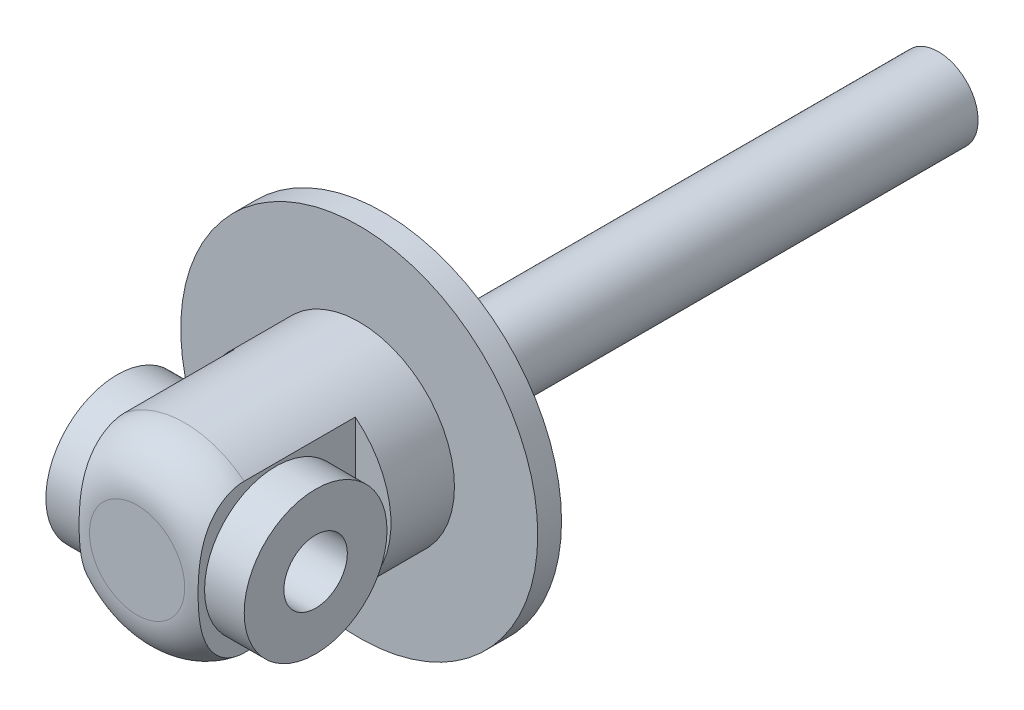
SolidWorks part; units mm, degrees
ref_plane "Front Plane" through (0, 0, 0) normal (0, 0, 1) x (1, 0, 0)
ref_plane "Top Plane" through (0, 0, 0) normal (0, 1, 0) x (1, 0, 0)
ref_plane "Right Plane" through (0, 0, 0) normal (1, 0, 0) x (0, 0, -1)
sketch "Sketch1" plane through (0, 0, 0) normal (0, 0, 1) x (1, 0, 0)
  circle A0 centre (0, 0) radius 22.5
  dimension "D1" = 45
extrude "Boss-Extrude1" add sketch "Sketch1" against normal blind 3
sketch "Sketch2" plane through (0, 0, -3) normal (0, 0, -1) x (-1, 0, 0)
  circle A0 centre (0, 0) radius 5
  dimension "D1" = 10
extrude "Boss-Extrude2" add sketch "Sketch2" along normal blind 70
sketch "Sketch3" plane through (0, 0, 0) normal (0, 0, 1) x (1, 0, 0)
  circle A0 centre (0, 0) radius 12
  dimension "D1" = 24
extrude "Boss-Extrude3" add sketch "Sketch3" along normal blind 28
fillet "Fillet1" radius 6 1 edges at (12, 0, 28)
sketch "Sketch4" plane through (0, 0, 0) normal (0, 1, 0) x (1, 0, 0)
  line L0 (0, 0) -> (0, -33.2547) construction
  line L1 (7.5, -28) -> (27.07, -28)
  line L2 (-6, -28) -> (6, -28) construction
  line L3 (27.07, -28) -> (27.07, -8)
  line L4 (27.07, -8) -> (7.5, -8)
  line L5 (7.5, -8) -> (7.5, -28)
  line L6 (-7.5, -8) -> (-7.5, -28)
  line L7 (-27.07, -8) -> (-7.5, -8)
  line L8 (-27.07, -28) -> (-27.07, -8)
  line L9 (-7.5, -28) -> (-27.07, -28)
  dimension "D1" = 15
  dimension "D2" = 20
  dimension "D3" = 19.57
extrude "Cut-Extrude1" cut sketch "Sketch4" against normal through all both and the other way through all
sketch "Sketch5" plane through (7.5, 0, 0) normal (1, 0, 0) x (0, 0, -1)
  line L0 (0, 0) -> (-27.8095, 0) construction
  line L1 (-28, 6) -> (-28, -6) construction
  circle A0 centre (-18, 0) radius 4
  spline S0 degree 3 poles (-22, 9.3675) (-22.256, 9.3675) (-22.5161, 9.346) (-23.0236, 9.2617) (-23.2718, 9.1993) (-23.7573, 9.0353) (-23.9966, 8.9325) (-24.4529, 8.6933) (-24.67, 8.5573) (-25.0836, 8.2544) (-25.2813, 8.0864) (-25.6506, 7.7261) (-25.8216, 7.5349) (-26.2977, 6.9312) (-26.5672, 6.4844) (-27.0045, 5.5607) (-27.1758, 5.0803) (-27.4469, 4.0917) (-27.5457, 3.5846) (-27.6899, 2.5722) (-27.7363, 2.0636) (-27.7958, 1.0432) (-27.8091, 0.5315) (-27.8098, -0.4943) (-27.797, -1.0101) (-27.7387, -2.0342) (-27.6929, -2.5445) (-27.5501, -3.56) (-27.4524, -4.0672) (-27.1812, -5.0646) (-27.0094, -5.5488) (-26.5703, -6.4792) (-26.3001, -6.9277) (-25.8239, -7.5323) (-25.6529, -7.7237) (-25.2839, -8.0841) (-25.0844, -8.2538) (-24.462, -8.7096) (-24.0109, -8.9491) (-23.2725, -9.1993) (-23.0206, -9.2623) (-22.5143, -9.3462) (-22.2585, -9.3675) (-22, -9.3675) knots 0 0 0 0 0.03125 0.03125 0.0625 0.0625 0.09375 0.09375 0.125 0.125 0.15625 0.15625 0.1875 0.1875 0.25 0.25 0.3125 0.3125 0.375 0.375 0.4375 0.4375 0.5 0.5 0.5625 0.5625 0.625 0.625 0.6875 0.6875 0.75 0.75 0.8125 0.8125 0.84375 0.84375 0.875 0.875 0.9375 0.9375 0.96875 0.96875 1 1 1 1 construction
  dimension "D1" = 8
  dimension "D2" = 10
extrude "Cut-Extrude2" cut sketch "Sketch5" against normal through all both and the other way through all
sketch "Sketch6" plane through (0, 0, 0) normal (1, 0, 0) x (0, 0, -1)
  circle A0 centre (-18, 0) radius 9
  circle A1 centre (-18, 0) radius 4 construction
  circle A2 centre (-18, 0) radius 4
  dimension "D1" = 18
extrude "Boss-Extrude4" add sketch "Sketch6" along normal mid plane 25
